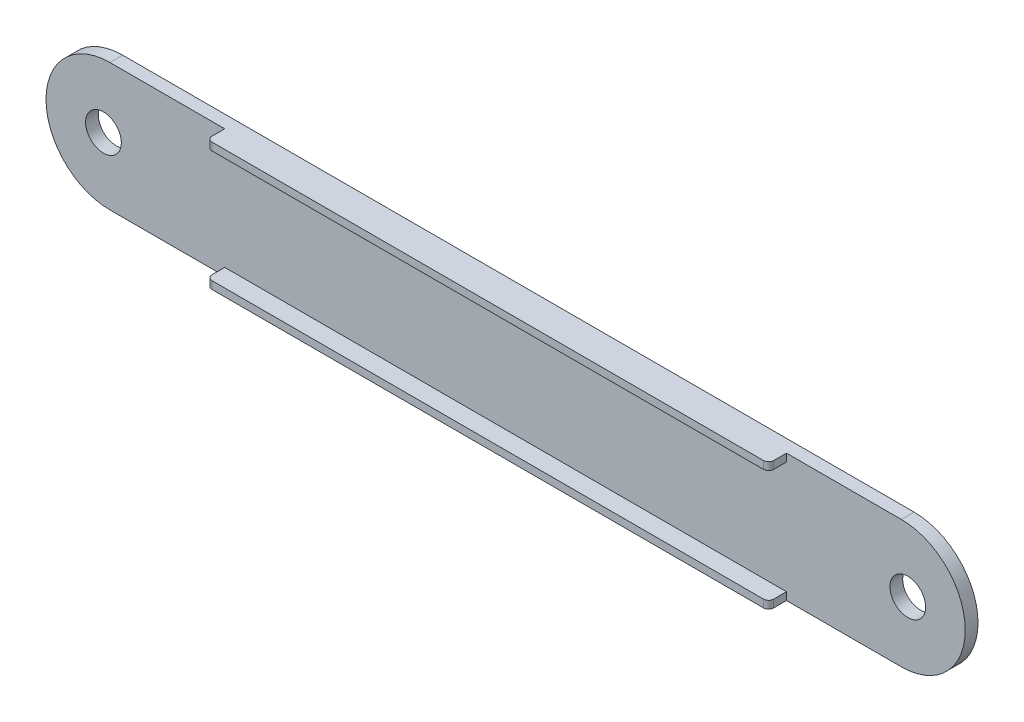
SolidWorks part; units mm, degrees
ref_plane "Front Plane" through (0, 0, 0) normal (0, 0, 1) x (1, 0, 0)
ref_plane "Top Plane" through (0, 0, 0) normal (0, 1, 0) x (1, 0, 0)
ref_plane "Right Plane" through (0, 0, 0) normal (1, 0, 0) x (0, 0, -1)
sketch "Sketch2" plane through (0, 0, 0) normal (0, 0, 1) x (1, 0, 0)
  line L0 (-142.959, 32.1822) -> (167.041, 32.1822)
  line L2 (-142.959, -17.8178) -> (167.041, -17.8178)
  arc A0 (-142.959, -17.8178) -> (-142.959, 32.1822) centre (-142.959, 7.1822) cw
  arc A1 (167.041, 32.1822) -> (167.041, -17.8178) centre (167.041, 7.1822) cw
  dimension "D1" = 310
  dimension "D2" = 50
extrude "Boss-Extrude1" add sketch "Sketch2" along normal blind 5
sketch "Sketch3" plane through (0, 0, 5) normal (0, 0, 1) x (1, 0, 0)
  line L0 (-142.959, 32.1822) -> (167.041, 32.1822)
  line L1 (167.041, 32.1822) -> (167.041, -17.8178)
  line L2 (167.041, -17.8178) -> (-142.959, -17.8178)
  line L3 (-142.959, -17.8178) -> (-142.959, 32.1822)
  line L4 (-97.959, 32.1822) -> (-97.959, 29.1822)
  line L5 (122.041, 32.1822) -> (122.041, 29.1822)
  line L6 (-97.959, 29.1822) -> (122.041, 29.1822)
  line L7 (-142.959, 7.1822) -> (192.041, 7.1822) construction
  line L8 (-97.959, -14.8178) -> (122.041, -14.8178)
  line L9 (122.041, -17.8178) -> (122.041, -14.8178)
  line L10 (-97.959, -17.8178) -> (-97.959, -14.8178)
  arc A0 (167.041, -17.8178) -> (167.041, 32.1822) centre (167.041, 7.1822) ccw construction
  dimension "D1" = 45
  dimension "D2" = 45
  dimension "D3" = 3
  dimension "D4" = 3
extrude "Boss-Extrude2" add sketch "Sketch3" along normal blind 7 contours L4 L6 L5 L0 | L10 L2 L9 L8
sketch "Sketch4" plane through (0, 0, 5) normal (0, 0, 1) x (1, 0, 0)
  line L0 (-142.959, 32.1822) -> (-142.959, 13.7206)
  line L1 (-142.959, -17.8178) -> (167.041, -17.8178)
  line L2 (167.041, -17.8178) -> (167.041, 0.6439)
  line L3 (167.041, 32.1822) -> (-142.959, 32.1822)
  line L4 (-152.459, 7.1822) -> (-167.959, 7.1822)
  line L5 (12.041, 29.1822) -> (12.041, -14.8178) construction
  line L6 (-97.959, 29.1822) -> (122.041, 29.1822) construction
  line L7 (-97.959, -14.8178) -> (122.041, -14.8178) construction
  line L8 (176.541, 7.1822) -> (192.041, 7.1822)
  line L9 (167.041, 32.1822) -> (167.041, 13.7206)
  line L10 (-142.959, 0.6439) -> (-142.959, -17.8178)
  line L11 (167.041, 13.7206) -> (167.041, 32.1822)
  line L12 (167.041, 0.6439) -> (167.041, -17.8178)
  arc A0 (-142.959, 32.1822) -> (-142.959, -17.8178) centre (-142.959, 7.1822) ccw
  circle A1 centre (-145.459, 7.1822) radius 7
  circle A2 centre (169.541, 7.1822) radius 7
  arc A3 (167.041, 32.1822) -> (167.041, -17.8178) centre (167.041, 7.1822) cw
  line M5 (-142.959, -17.8178) -> (-97.959, -17.8178)
  dimension "D1" = 2.5
  dimension "D2" = 14
extrude "Cut-Extrude1" cut sketch "Sketch4" against normal blind 7 contours A1 | A2 M5
sketch "Sketch5" plane through (0, -17.8178, 0) normal (0, -1, 0) x (1, 0, 0)
  line L0 (-97.959, 5) -> (-97.959, 10)
  line L1 (-95.959, 12) -> (120.041, 12)
  line L2 (122.041, 10) -> (122.041, 5)
  line L3 (-97.959, 10) -> (-97.959, 12)
  line L4 (-97.959, 12) -> (-95.959, 12)
  line L5 (120.041, 12) -> (122.041, 12)
  line L6 (122.041, 12) -> (122.041, 10)
  arc A0 (-97.959, 10) -> (-95.959, 12) centre (-95.959, 10) cw
  arc A1 (122.041, 10) -> (120.041, 12) centre (120.041, 10) ccw
  point P10 (-97.959, 12)
  point P13 (122.041, 12)
  line M4 (122.041, 5) -> (122.041, 12)
  line M5 (122.041, 12) -> (-97.959, 12)
  line M6 (-97.959, 12) -> (-97.959, 5)
  dimension "D1" = 2
  dimension "D2" = 2
extrude "Cut-Extrude2" cut sketch "Sketch5" against normal blind 70 contours A0 M6 M5 | A1 M4 M5
